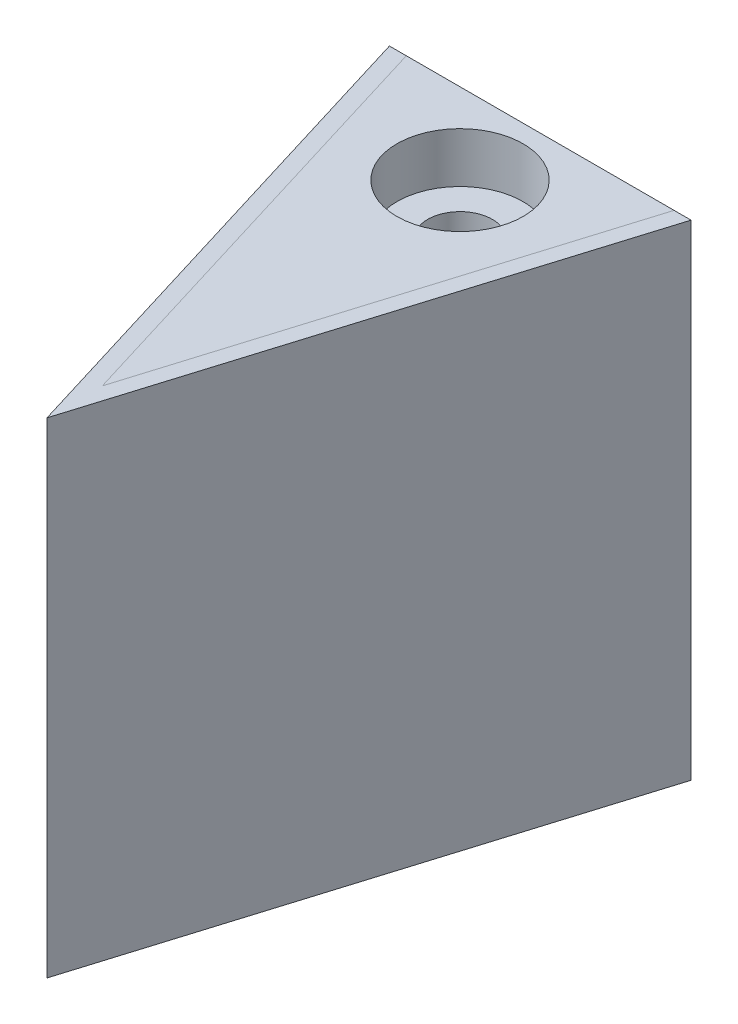
SolidWorks part; units mm, degrees
material "Plain Carbon Steel"
ref_plane "Front Plane" through (0, 0, 0) normal (0, 0, 1) x (1, 0, 0)
ref_plane "Top Plane" through (0, 0, 0) normal (0, 1, 0) x (1, 0, 0)
ref_plane "Right Plane" through (0, 0, 0) normal (1, 0, 0) x (0, 0, -1)
sketch "Sketch1" plane through (0, 0, 0) normal (0, 1, 0) x (1, 0, 0)
  line L0 (4.6424, -4.5654) -> (-4.6824, -4.5654)
  line L1 (-1.0137, -16.5654) -> (-4.6824, -4.5654)
  line L2 (-0.02, -19.8154) -> (-0.02, -4.5654) construction
  line L3 (0.9736, -16.5654) -> (4.6424, -4.5654)
  line L4 (-1.0137, -16.5654) -> (0.9736, -16.5654) construction
  line L8 (0.9736, -16.5654) -> (-0.02, -19.8154)
  line L9 (-0.02, -19.8154) -> (-1.0137, -16.5654)
  point P2 (-0.02, -16.5654)
  point P8 (-0.0154, 5.3291)
  dimension "D1" = 17
  dimension "D2" = 3.25
  dimension "D3" = 12
  dimension "D6" = 17
extrude "Boss-Extrude1" add sketch "Sketch1" along normal blind 12.5 and the other way blind 2.5
sketch "Sketch2" plane through (0, 0, 4.5654) normal (0, 0, -1) x (-1, 0, 0)
  line L0 (-4.6424, 12.5) -> (4.6824, -2.5) construction
  line L1 (4.6824, 12.5) -> (-4.6424, -2.5) construction
  line L3 (-2.8782, 5.95) -> (2.9183, 5.95)
  line L5 (-2.8782, 4.05) -> (2.9183, 4.05)
  arc A0 (-2.8782, 4.05) -> (2.9183, 4.05) centre (0.02, 5) ccw
  arc A1 (2.9183, 5.95) -> (-2.8782, 5.95) centre (0.02, 5) ccw
  dimension "D1" = 1.9
extrude "Cut-Extrude1" cut sketch "Sketch2" against normal blind 5
ref_plane "Plane2" through (0, 0, 10.0654) normal (0, 0, -1) x (-1, 0, 0)
ref_plane "Plane4" through (0, 0, 10.0654) normal (0, 0, -1) x (-1, 0, 0)
sketch "Sketch5" plane through (0, 5.74, 0) normal (0, 1, 0) x (1, 0, 0)
  line L3 (0.9955, -10.0654) -> (-0.9955, -10.0654) construction
  line L4 (4.6424, -4.5654) -> (-4.6824, -4.5654) construction
  circle A0 centre (0, -7.0654) radius 1
  dimension "D1" = 3
  dimension "D2" = 2.5
extrude "Cut-Extrude2" cut sketch "Sketch5" against normal through all and the other way through all
sketch "Sketch6" plane through (0, 12.5, 0) normal (0, 1, 0) x (1, 0, 0)
  circle A0 centre (0, -7.0654) radius 1.95
extrude "Cut-Extrude3" cut sketch "Sketch6" against normal blind 1.55 contours A0
sketch "Sketch7" plane through (0, 12.5, 0) normal (0, 1, 0) x (1, 0, 0)
  line L0 (-4.6824, -4.5654) -> (-0.02, -19.8154)
  line L2 (-0.02, -19.8154) -> (4.6424, -4.5654)
  line L4 (-4.1596, -4.5654) -> (-0.02, -18.1052)
  line L6 (-0.02, -18.1052) -> (4.1195, -4.5654)
  line L7 (-4.6824, -4.5654) -> (-4.1596, -4.5654)
  line L8 (4.6424, -4.5654) -> (4.1195, -4.5654)
  line L9 (4.6424, -4.5654) -> (-4.6824, -4.5654) construction
  line L10 (-0.02, -18.1052) -> (4.1642, -4.4192) construction
  line L11 (-4.2043, -4.4192) -> (-0.02, -18.1052) construction
  dimension "D1" = 0.5
split "Split3" trim tools "Sketch7" bodies to split 114 resulting bodies 119 120
